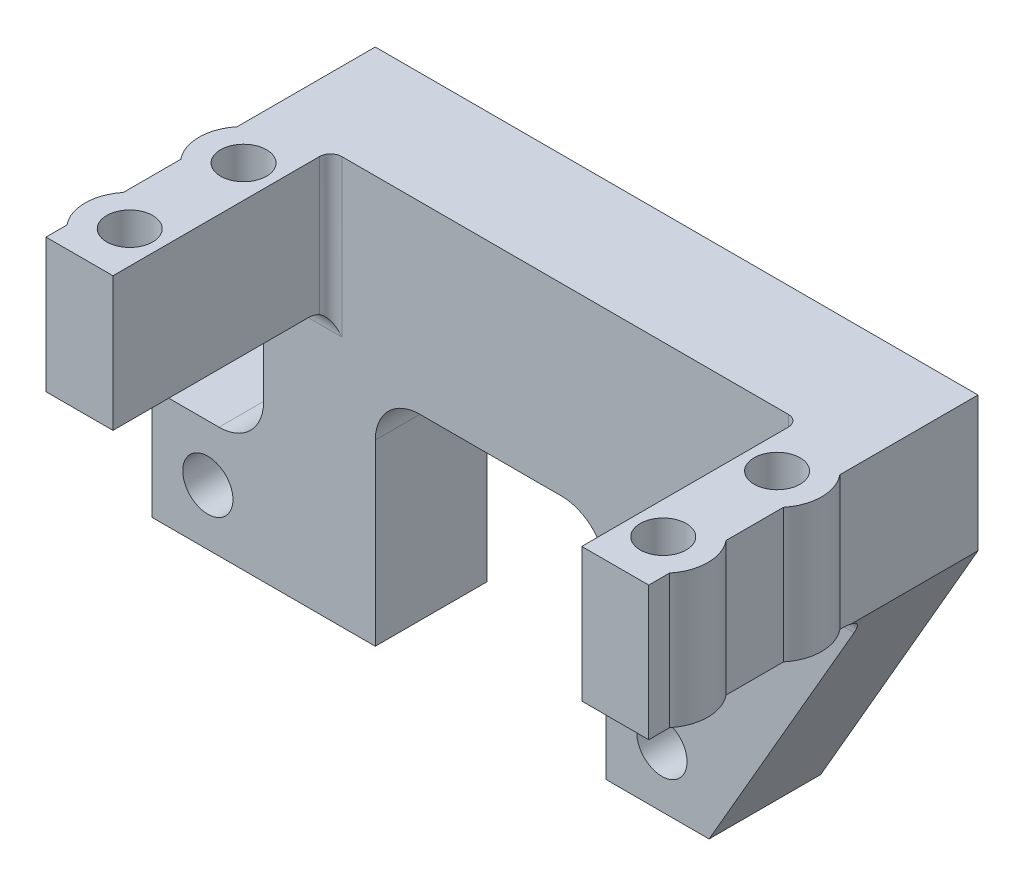
SolidWorks part; units mm, degrees
ref_plane "Front Plane" through (0, 0, 0) normal (0, 0, 1) x (1, 0, 0)
ref_plane "Top Plane" through (0, 0, 0) normal (0, 1, 0) x (1, 0, 0)
ref_plane "Right Plane" through (0, 0, 0) normal (1, 0, 0) x (0, 0, -1)
sketch "Sketch1" plane through (0, 0, 0) normal (0, 0, 1) x (1, 0, 0)
  line L1 (-27, 13.25) -> (27, 13.25)
  line L2 (-27, 13.25) -> (-27, -13.25)
  line L3 (-27, -13.25) -> (27, -13.25)
  line L4 (27, 13.25) -> (27, -13.25)
  dimension "D1" = 54
  dimension "D2" = 27
  dimension "D3" = 26.5
  dimension "D4" = 13.25
extrude "Boss-Extrude1" add sketch "Sketch1" along normal blind 10
sketch "Sketch2" plane through (0, 0, 0) normal (0, 0, -1) x (-1, 0, 0)
  line L1 (-27, 1.161) -> (-18.6798, -13.25)
  line L2 (27, -13.25) -> (-27, -13.25) construction
  line L3 (-18.6798, -13.25) -> (-27, -13.25)
  line L4 (-27, -13.25) -> (-27, 13.25) construction
  line L5 (-27, -13.25) -> (-27, 1.161)
extrude "Cut-Extrude1" cut sketch "Sketch2" against normal blind 10
sketch "Sketch3" plane through (0, -13.25, 0) normal (0, -1, 0) x (1, 0, 0)
  line L0 (-27, 0) -> (18.6798, 0) construction
  line L1 (18.6798, 10) -> (3.6798, 10)
  line L2 (18.6798, 10) -> (18.6798, 0)
  line L3 (18.6798, 0) -> (3.6798, 0)
  line L4 (3.6798, 10) -> (3.6798, 0)
  line L6 (-27, 10) -> (-17, 10)
  line L7 (-27, 10) -> (-27, 0)
  line L8 (-27, 0) -> (-17, 0)
  line L9 (-17, 10) -> (-17, 0)
  dimension "D1" = 10
  dimension "D2" = 15
extrude "Boss-Extrude2" add sketch "Sketch3" along normal blind 10
sketch "Sketch4" plane through (0, 0, 0) normal (0, 0, -1) x (-1, 0, 0)
  line L1 (-18.6798, -13.25) -> (-12.9063, -23.25)
  line L2 (-3.6798, -23.25) -> (-18.6798, -23.25) construction
  line L3 (-12.9063, -23.25) -> (-18.6798, -23.25)
  line L4 (-18.6798, -23.25) -> (-18.6798, -13.25) construction
  line L5 (-18.6798, -23.25) -> (-18.6798, -13.25)
extrude "Cut-Extrude2" cut sketch "Sketch4" against normal blind 10
sketch "Sketch5" plane through (0, 0, 0) normal (0, 0, -1) x (-1, 0, 0)
  line L0 (17, -13.25) -> (-3.6798, -13.25) construction
  line L1 (17, -13.25) -> (-3.6798, -13.25)
  line L2 (17, -13.25) -> (17, -8.25)
  line L3 (17, -8.25) -> (-3.6798, -8.25)
  line L4 (-3.6798, -8.25) -> (-3.6798, -13.25)
  dimension "D1" = 5
extrude "Cut-Extrude3" cut sketch "Sketch5" against normal blind 10
sketch "Sketch6" plane through (0, 0, 10) normal (0, 0, 1) x (1, 0, 0)
  line L1 (27, 13.25) -> (21, 13.25)
  line L2 (27, 13.25) -> (27, 1.25)
  line L3 (27, 1.25) -> (21, 1.25)
  line L4 (21, 13.25) -> (21, 1.25)
  dimension "D1" = 6
  dimension "D2" = 12
extrude "Boss-Extrude3" add sketch "Sketch6" along normal blind 19.5
sketch "Sketch7" plane through (0, 13.25, 0) normal (0, 1, 0) x (1, 0, 0)
  line L0 (27, -29.5) -> (27, 0) construction
  line L1 (27, -29.5) -> (21, -29.5) construction
  circle A4 centre (23.9, -25.1) radius 2.06
  circle A5 centre (23.9, -14.9) radius 2.06
  dimension "D1" = 4.12
  dimension "D2" = 4.12
  dimension "D5" = 10.2
  dimension "D3" = 3.1
  dimension "D4" = 4.4
extrude "Cut-Extrude4" cut sketch "Sketch7" against normal through all
sketch "Sketch8" plane through (0, 13.25, 0) normal (0, 1, 0) x (1, 0, 0)
  line L0 (21, -29.5) -> (21, -10) construction
  line L1 (21, -27.855) -> (21, -22.345)
  line L2 (21, -17.655) -> (21, -12.145)
  circle A0 centre (23.9, -25.1) radius 2.06
  arc A1 (21, -27.855) -> (21, -22.345) centre (23.9, -25.1) ccw
  circle A2 centre (23.9, -14.9) radius 2.06
  arc A3 (21, -17.655) -> (21, -12.145) centre (23.9, -14.9) ccw
  dimension "D1" = 8
  dimension "D2" = 8
extrude "Boss-Extrude4" add sketch "Sketch8" against normal up to surface (12 mm away) up to face at (21.84, 1.25, 25.1)
fillet "Fillet1" radius 2 2 edges at (27, 1.2055, 10) (24, 1.25, 10)
fillet "Fillet2" radius 1 1 edges at (21, 6.25, 10)
ref_plane "Plane1" through (0, 0, 0) normal (1, 0, 0) x (0, 0, -1)
mirror "Mirror1" about plane through (0, 0, 0) normal (1, 0, 0) of "Fillet2", "Boss-Extrude4", "Boss-Extrude3", "Cut-Extrude4", "Fillet1", "Boss-Extrude1"
sketch "Sketch9" plane through (0, 0, 10) normal (0, 0, 1) x (1, 0, 0)
  line L0 (3.6798, -23.25) -> (3.6798, -13.25) construction
  line L1 (12.9063, -23.25) -> (3.6798, -23.25) construction
  circle A0 centre (8.6798, -18.25) radius 2.25
  dimension "D2" = 4.5
  dimension "D3" = 5
  dimension "D4" = 5
extrude "Cut-Extrude5" cut sketch "Sketch9" against normal blind 10
sketch "Sketch10" plane through (0, 0, 0) normal (0, 0, -1) x (-1, 0, 0)
  line L1 (-27, 1.161) -> (-18.6798, -13.25)
  line L2 (-27, -13.25) -> (-27, 13.25) construction
  line L3 (-27, -13.25) -> (-27, 1.161)
  line L4 (-27, -13.25) -> (-18.6798, -13.25) construction
  line L5 (-27, -13.25) -> (-18.6798, -13.25)
extrude "Cut-Extrude6" cut sketch "Sketch10" against normal blind 10
sketch "Sketch11" plane through (0, 0, 0) normal (0, 0, -1) x (-1, 0, 0)
  line L0 (-3.6798, -23.25) -> (-3.6798, -13.25) construction
  line L1 (17, -13.25) -> (-3.6798, -13.25)
  line L2 (17, -13.25) -> (17, -3.25)
  line L3 (17, -3.25) -> (-3.6798, -3.25)
  line L4 (-3.6798, -13.25) -> (-3.6798, -3.25)
  dimension "D1" = 10
extrude "Cut-Extrude7" cut sketch "Sketch11" against normal blind 10
fillet "Fillet3" radius 4 2 edges at (3.6798, -3.25, 5) (-17, -3.25, 5)
sketch "Sketch12" plane through (0, 0, 10) normal (0, 0, 1) x (1, 0, 0)
  line L1 (-27, -23.25) -> (-37, -23.25)
  line L2 (-27, -23.25) -> (-27, -13.25)
  line L3 (-27, -13.25) -> (-37, -13.25)
  line L4 (-37, -23.25) -> (-37, -13.25)
  dimension "D1" = 10
  dimension "D2" = 10
extrude "Boss-Extrude5" add sketch "Sketch12" against normal blind 10
sketch "Sketch13" plane through (0, 0, 10) normal (0, 0, 1) x (1, 0, 0)
  line L1 (-37, -13.25) -> (-37, -23.25) construction
  line L2 (-17, -23.25) -> (-37, -23.25) construction
  circle A0 centre (-32, -18.25) radius 2.25
  dimension "D1" = 4.5
  dimension "D2" = 5
  dimension "D3" = 5
extrude "Cut-Extrude8" cut sketch "Sketch13" against normal blind 10
fillet "Fillet4" radius 4 1 edges at (-27, -13.25, 5)
